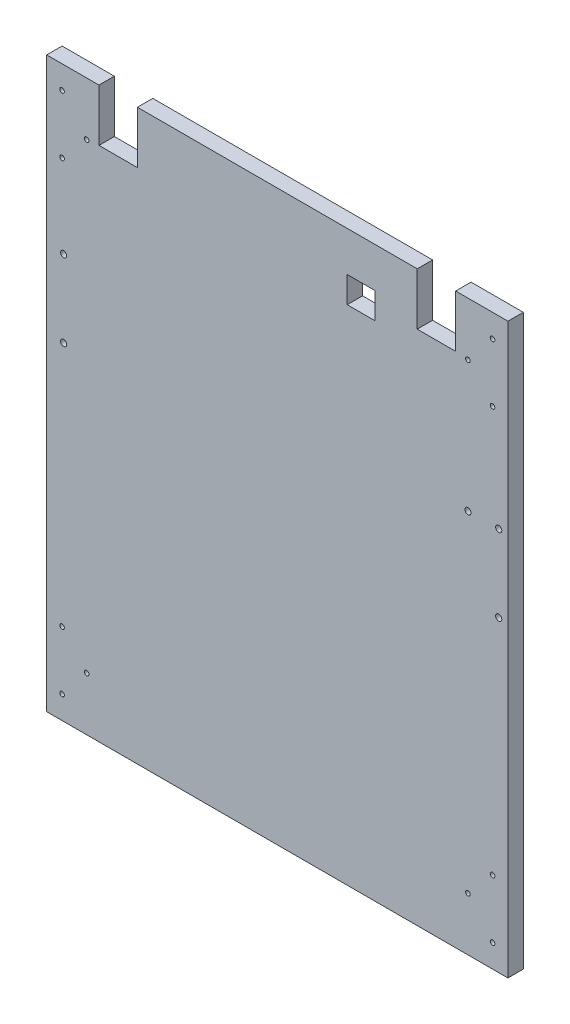
SolidWorks part; units mm, degrees
ref_plane "前视基准面" through (0, 0, 0) normal (0, 0, 1) x (1, 0, 0)
ref_plane "上视基准面" through (0, 0, 0) normal (0, 1, 0) x (1, 0, 0)
ref_plane "右视基准面" through (0, 0, 0) normal (1, 0, 0) x (0, 0, -1)
sketch "草图1" plane through (0, 0, 0) normal (0, 0, 1) x (1, 0, 0)
  line L1 (-36.0018, 390.5547) -> (263.9982, 390.5547)
  line L2 (-36.0018, 390.5547) -> (-36.0018, 20.5547)
  line L3 (-36.0018, 20.5547) -> (263.9982, 20.5547)
  line L4 (263.9982, 390.5547) -> (263.9982, 20.5547)
extrude "凸台-拉伸1" add sketch "草图1" along normal blind 10
sketch "草图2" plane through (0, 0, 10) normal (0, 0, 1) x (1, 0, 0)
  line L0 (263.9982, 390.5547) -> (253.9982, 390.5547) construction
  line L1 (263.9982, 390.5547) -> (-36.0018, 390.5547) construction
  line L2 (263.9982, 20.5547) -> (263.9982, 390.5547) construction
  line L3 (253.9982, 390.5547) -> (253.9982, 375.5547) construction
  line L4 (253.9982, 375.5547) -> (253.9982, 337.5547) construction
  line L5 (113.9982, 390.5547) -> (113.9982, 20.5547) construction
  line L6 (-36.0018, 20.5547) -> (263.9982, 20.5547) construction
  line L7 (263.9982, 205.5547) -> (-36.0018, 205.5547) construction
  line L8 (-36.0018, 390.5547) -> (-36.0018, 20.5547) construction
  line L9 (-26.0018, 375.5547) -> (-26.0018, 337.5547) construction
  line L10 (-26.0018, 390.5547) -> (-26.0018, 375.5547) construction
  line L11 (-36.0018, 390.5547) -> (-26.0018, 390.5547) construction
  line L12 (-36.0018, 20.5547) -> (-26.0018, 20.5547) construction
  line L13 (-26.0018, 20.5547) -> (-26.0018, 35.5547) construction
  line L14 (-26.0018, 35.5547) -> (-26.0018, 73.5547) construction
  line L15 (253.9982, 35.5547) -> (253.9982, 73.5547) construction
  line L16 (253.9982, 20.5547) -> (253.9982, 35.5547) construction
  line L17 (263.9982, 20.5547) -> (253.9982, 20.5547) construction
  line L18 (253.9982, 390.5547) -> (237.9982, 390.5547) construction
  line L19 (237.9982, 390.5547) -> (237.9982, 385.8047) construction
  line L20 (237.9982, 385.8047) -> (237.9982, 355.8047) construction
  line L21 (237.9982, 355.8047) -> (237.9982, 336.8047) construction
  line L22 (263.9982, 390.5547) -> (229.9982, 390.5547) construction
  line L23 (229.9982, 390.5547) -> (229.9982, 356.5547)
  line L24 (229.9982, 356.5547) -> (204.9982, 356.5547)
  line L25 (204.9982, 356.5547) -> (204.9982, 390.5547)
  line L26 (204.9982, 390.5547) -> (229.9982, 390.5547)
  line L27 (-36.0018, 390.5547) -> (-2.0018, 390.5547) construction
  line L28 (22.9982, 356.5547) -> (22.9982, 390.5547)
  line L29 (-2.0018, 356.5547) -> (22.9982, 356.5547)
  line L30 (-2.0018, 390.5547) -> (-2.0018, 356.5547)
  line L31 (22.9982, 390.5547) -> (-2.0018, 390.5547)
  line L32 (237.9982, 270.5547) -> (263.9982, 270.5547) construction
  line L33 (263.9982, 270.5547) -> (257.9982, 270.5547) construction
  line L34 (168.4556, 390.5547) -> (168.4556, 355.5547) construction
  line L35 (168.4556, 355.5547) -> (150.4556, 355.5547) construction
  line L36 (159.4556, 355.5547) -> (159.4556, 364.5547)
  line L37 (159.4556, 364.5547) -> (177.4556, 364.5547)
  line L38 (177.4556, 364.5547) -> (177.4556, 356.5547)
  line L39 (177.4556, 356.5547) -> (177.4556, 347.5547)
  line L40 (177.4556, 347.5547) -> (159.4556, 347.5547)
  line L41 (159.4556, 347.5547) -> (159.4556, 355.5547)
  line L42 (257.9982, 270.5547) -> (257.9982, 320.5547) construction
  line L43 (257.9982, 270.5547) -> (257.9982, 220.5547) construction
  line L44 (-4.9801, 283.808) -> (-24.9801, 283.808) construction
  line L45 (-24.9801, 283.808) -> (-24.9801, 333.808) construction
  line L46 (-24.9801, 333.808) -> (-24.9801, 233.808) construction
  circle A0 centre (253.9982, 375.5547) radius 1.5
  circle A1 centre (253.9982, 337.5547) radius 1.5
  circle A2 centre (-26.0018, 337.5547) radius 1.5
  circle A3 centre (-26.0018, 375.5547) radius 1.5
  circle A4 centre (-26.0018, 35.5547) radius 1.5
  circle A5 centre (-26.0018, 73.5547) radius 1.5
  circle A6 centre (253.9982, 73.5547) radius 1.5
  circle A7 centre (253.9982, 35.5547) radius 1.5
  circle A8 centre (237.9982, 355.8047) radius 1.5
  circle A9 centre (-10.0018, 355.8047) radius 1.5
  circle A10 centre (-10.0018, 55.3047) radius 1.5
  circle A11 centre (237.9982, 55.3047) radius 1.5
  circle A12 centre (237.9982, 270.5547) radius 2
  circle A15 centre (257.9982, 270.5547) radius 2
  circle A17 centre (257.9982, 220.5547) radius 2
  circle A18 centre (-24.9801, 233.808) radius 2
  circle A20 centre (-24.9801, 283.808) radius 2
  dimension "D3" = 3
  dimension "D5" = 3
  dimension "D8" = 3
  dimension "D14" = 4
  dimension "D16" = 4
  dimension "D26" = 4
  dimension "D30" = 4
  dimension "D32" = 4
  dimension "D1" = 10
  dimension "D2" = 15
  dimension "D4" = 38
  dimension "D6" = 16
  dimension "D7" = 30
  dimension "D9" = 19
  dimension "D10" = 34
  dimension "D11" = 34
  dimension "D12" = 25
  dimension "D13" = 120
  dimension "D15" = 6
  dimension "D17" = 35
  dimension "D18" = 18
  dimension "D19" = 9
  dimension "D20" = 18
  dimension "D21" = 8
  dimension "D22" = 9
  dimension "D23" = 50
  dimension "D25" = 50
  dimension "D28" = 50
  dimension "D29" = 100
extrude "切除-拉伸1" cut sketch "草图2" against normal blind 10
